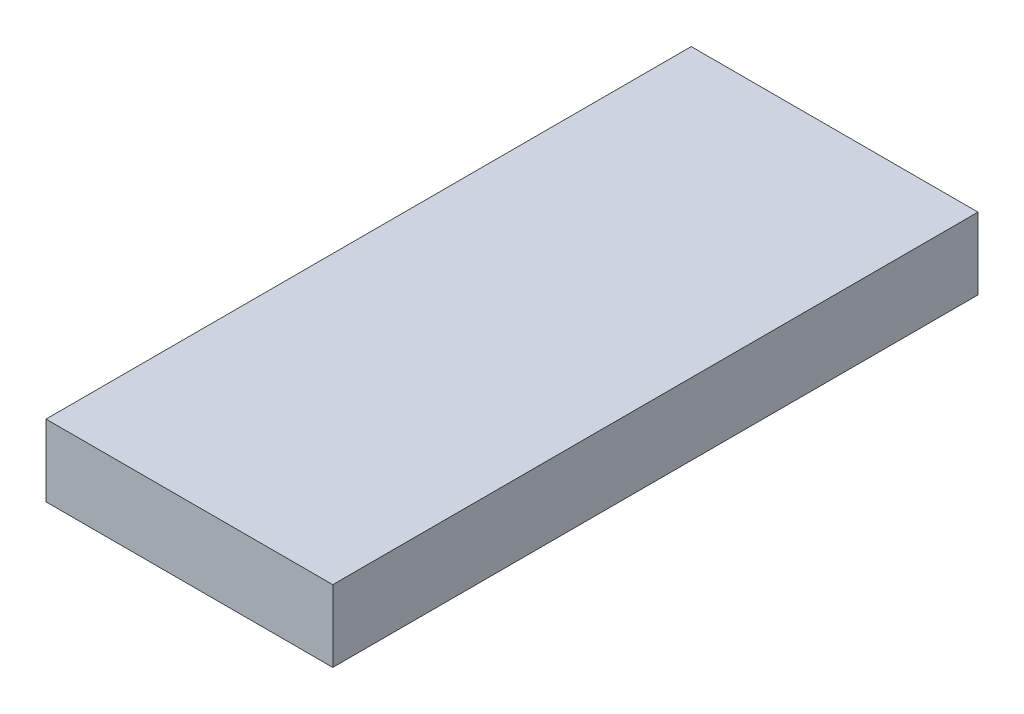
SolidWorks part; units mm, degrees
ref_plane "Front Plane" through (0, 0, 0) normal (0, 0, 1) x (1, 0, 0)
ref_plane "Top Plane" through (0, 0, 0) normal (0, 1, 0) x (1, 0, 0)
ref_plane "Right Plane" through (0, 0, 0) normal (1, 0, 0) x (0, 0, -1)
sketch "Sketch1" plane through (0, 0, 0) normal (0, 1, 0) x (1, 0, 0)
  line L1 (-10, 22.5) -> (10, 22.5)
  line L2 (-10, 22.5) -> (-10, -22.5)
  line L3 (-10, -22.5) -> (10, -22.5)
  line L4 (10, 22.5) -> (10, -22.5)
  line L5 (-10, 22.5) -> (10, -22.5) construction
  line L6 (-10, -22.5) -> (10, 22.5) construction
  point P0 (0, 0)
  dimension "D1" = 45
  dimension "D2" = 20
extrude "Boss-Extrude1" add sketch "Sketch1" along normal blind 5
